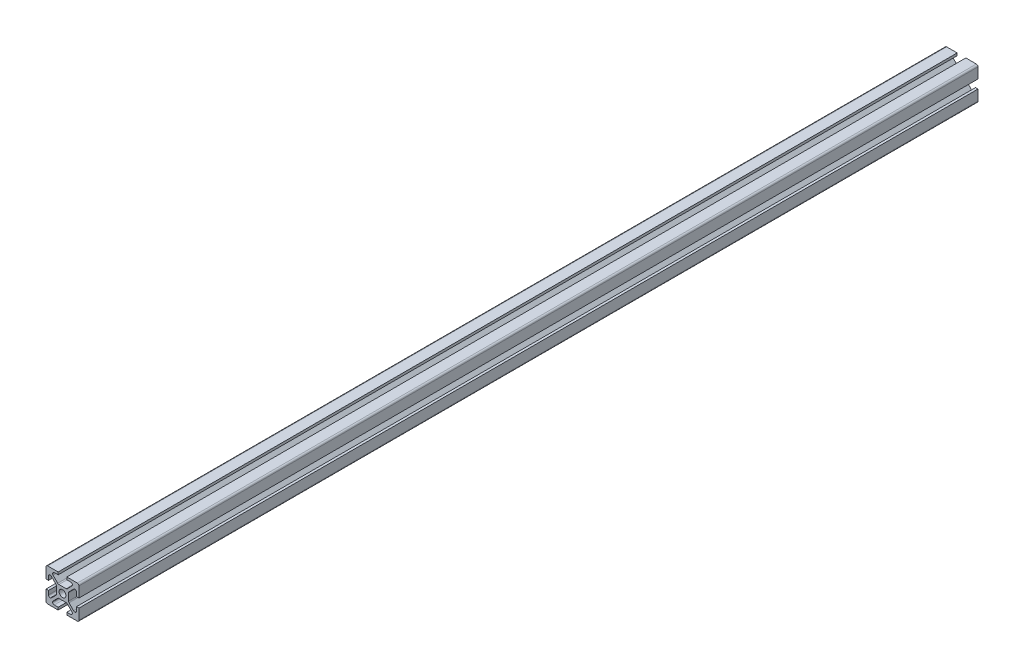
SolidWorks part; units mm, degrees
material "6061-T6 (SS)"
ref_plane "Front Plane" through (0, 0, 0) normal (0, 0, 1) x (1, 0, 0)
ref_plane "Top Plane" through (0, 0, 0) normal (0, 1, 0) x (1, 0, 0)
ref_plane "Right Plane" through (0, 0, 0) normal (1, 0, 0) x (0, 0, -1)
sketch "Sketch1" plane through (0, 0, 0) normal (0, 0, 1) x (1, 0, 0)
  line L0 (-10, 10) -> (10, -10) construction
  line L1 (-9, 10) -> (9, 10)
  line L2 (-10, 9) -> (-10, -9)
  line L3 (-9, -10) -> (9, -10)
  line L4 (10, 9) -> (10, -9)
  circle A0 centre (0, 0) radius 2.06
  arc A1 (-10, -9) -> (-9, -10) centre (-9, -9) ccw
  arc A2 (9, 10) -> (10, 9) centre (9, 9) cw
  arc A3 (10, -9) -> (9, -10) centre (9, -9) cw
  arc A4 (-9, 10) -> (-10, 9) centre (-9, 9) ccw
  dimension "D2" = 4.12
  dimension "D3" = 1
  dimension "D1" = 20
extrude "Boss-Extrude1" add sketch "Sketch1" along normal mid plane 545
sketch "Sketch2" plane through (0, 0, -272.5) normal (0, 0, -1) x (-1, 0, 0)
  line L0 (-10, 2.63) -> (-8.5, 2.63)
  line L1 (-10, -9) -> (-10, 9) construction
  line L2 (-8.5, 2.63) -> (-8.5, 4.995)
  line L3 (-6.7628, 5.7021) -> (-3.9479, 2.8872)
  line L4 (-3.655, 2.1801) -> (-3.655, -2.1801)
  line L5 (-3.9479, -2.8872) -> (-6.7628, -5.7021)
  line L6 (-8.5, -4.995) -> (-8.5, -2.63)
  line L7 (-8.5, -2.63) -> (-10, -2.63)
  line L8 (-10, -2.63) -> (-10, 2.63)
  line L9 (-10, 0) -> (-3.655, 0) construction
  line L10 (-3.655, 0) -> (0, 0) construction
  line L11 (-9, 9) -> (9, -9) construction
  line L12 (-9, -9) -> (9, 9) construction
  line L13 (-7.5, 5.995) -> (-7.4699, 5.995)
  line L14 (-7.5, -5.995) -> (-7.4699, -5.995)
  arc A0 (-7.5, 5.995) -> (-8.5, 4.995) centre (-7.5, 4.995) ccw
  arc A1 (-7.4699, 5.995) -> (-6.7628, 5.7021) centre (-7.4699, 4.995) cw
  arc A2 (-3.9479, 2.8872) -> (-3.655, 2.1801) centre (-4.655, 2.1801) cw
  arc A3 (-3.655, -2.1801) -> (-3.9479, -2.8872) centre (-4.655, -2.1801) cw
  arc A4 (-7.4699, -5.995) -> (-6.7628, -5.7021) centre (-7.4699, -4.995) ccw
  arc A5 (-7.5, -5.995) -> (-8.5, -4.995) centre (-7.5, -4.995) cw
  dimension "D6" = 1
  dimension "D1" = 3.655
  dimension "D2" = 0.75
  dimension "D3" = 1.5
  dimension "D4" = 5.26
  dimension "D5" = 11.99
extrude "Cut-Extrude1" cut sketch "Sketch2" against normal through all
pattern_circular "CirPattern1" count 4 over 360 about axis through (0, 0, 0) along (0, 0, 1) of "Cut-Extrude1"
